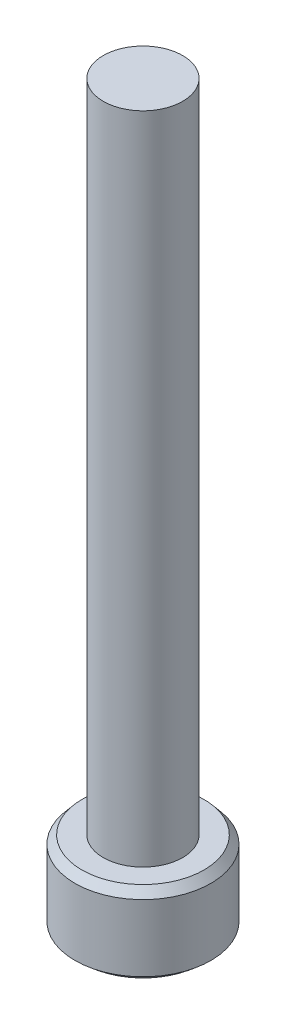
SolidWorks part; units mm, degrees
ref_plane "Front Plane" through (0, 0, 0) normal (0, 0, 1) x (1, 0, 0)
ref_plane "Top Plane" through (0, 0, 0) normal (0, 1, 0) x (1, 0, 0)
ref_plane "Right Plane" through (0, 0, 0) normal (1, 0, 0) x (0, 0, -1)
sketch "Sketch1" plane through (0, 0, 0) normal (0, 1, 0) x (1, 0, 0)
  circle A0 centre (0, 0) radius 4.15
  dimension "D1" = 8.3
extrude "Boss-Extrude1" add sketch "Sketch1" along normal blind 5
sketch "Sketch2" plane through (0, 5, 0) normal (0, 1, 0) x (1, 0, 0)
  circle A0 centre (0, 0) radius 2.425
  dimension "D1" = 4.85
extrude "Boss-Extrude2" add sketch "Sketch2" along normal blind 40
cosmetic thread "Cosmetic Thread1" [suppressed]
cosmetic thread "Cosmetic Thread2" [suppressed]
cosmetic thread "Cosmetic Thread3" [suppressed]
cosmetic thread "Cosmetic Thread4"
sketch "Sketch3" plane through (0, 0, 0) normal (0, -1, 0) x (1, 0, 0)
  line L1 (0, 2.786) -> (-2.4128, 1.393)
  line L2 (-2.4128, 1.393) -> (-2.4128, -1.393)
  line L3 (-2.4128, -1.393) -> (0, -2.786)
  line L4 (0, -2.786) -> (2.4128, -1.393)
  line L5 (2.4128, -1.393) -> (2.4128, 1.393)
  line L6 (2.4128, 1.393) -> (0, 2.786)
  circle A0 centre (0, 0) radius 2.4128 construction
extrude "Cut-Extrude1" cut sketch "Sketch3" against normal blind 3
chamfer "Chamfer1" distance 0.5 angle 40 2 edges at (0, 0, 4.15) (0, 5, 4.15)
